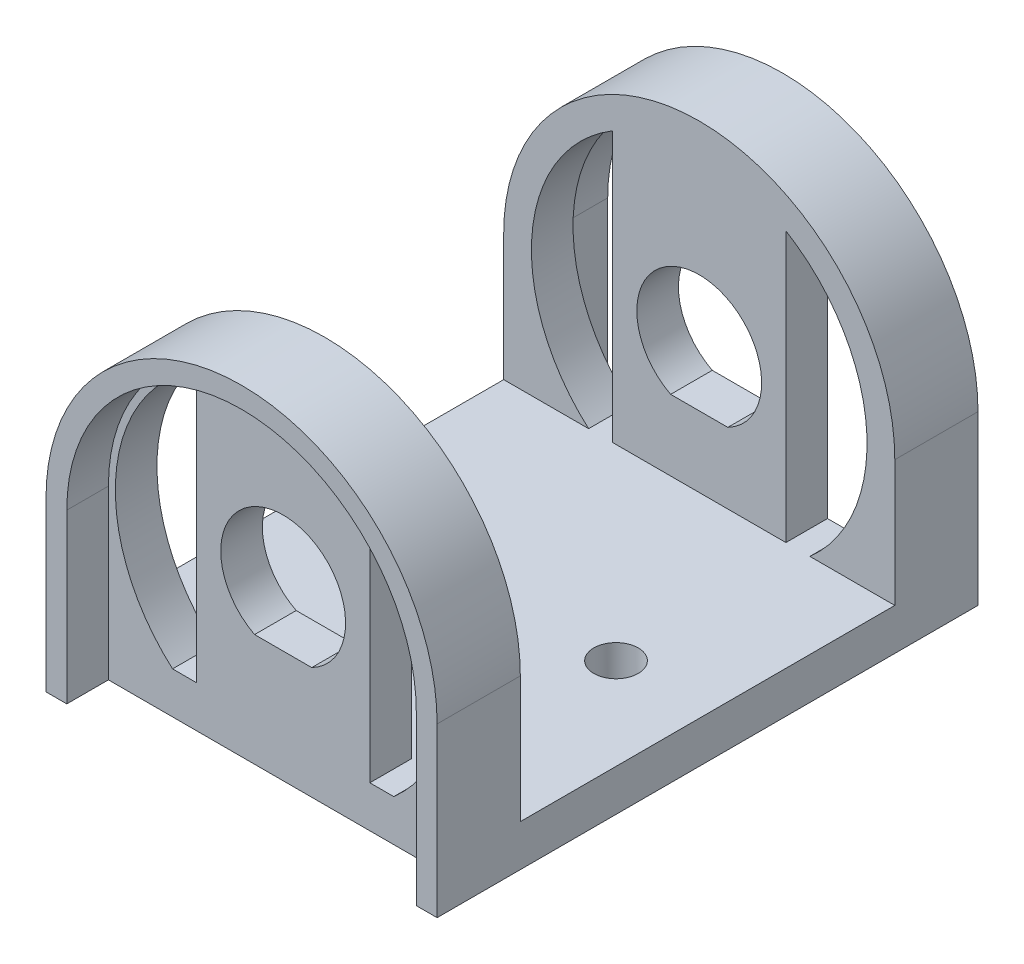
SolidWorks part; units mm, degrees
ref_plane "Front Plane" through (0, 0, 0) normal (0, 0, 1) x (1, 0, 0)
ref_plane "Top Plane" through (0, 0, 0) normal (0, 1, 0) x (1, 0, 0)
ref_plane "Right Plane" through (0, 0, 0) normal (1, 0, 0) x (0, 0, -1)
sketch "Sketch2" plane through (0, 0, 0) normal (0, 0, 1) x (1, 0, 0)
  line L0 (2, -4.75) -> (-2, -4.75) construction
  line L1 (-14.1, -13.1) -> (14.1, -13.1)
  line L3 (-14.1, 13.1) -> (14.1, 13.1) construction
  line L6 (0, -55) -> (0, 55) construction
  line L7 (2, -4.75) -> (-2, -4.75) construction
  line L8 (2.4495, -6.75) -> (-2.4495, -6.75) construction
  line L9 (6.25, 9.3609) -> (6.25, -10.1)
  line L10 (-6.25, 9.3609) -> (-6.25, -10.1)
  line L11 (7.975, -10.1) -> (6.25, -10.1)
  line L12 (-6.25, -10.1) -> (-7.975, -10.1)
  line L13 (2.0616, -5) -> (-2.0616, -5)
  line L27 (-14.1, 13.1) -> (14.1, -13.1) construction
  line L32 (14.1, 13.1) -> (-14.1, -13.1) construction
  line L35 (-14.1, -13.1) -> (-14.1, -1)
  line L36 (14.1, -13.1) -> (14.1, -1)
  line L37 (14.1, -1) -> (14.1, -13.1) construction
  line L38 (-14.1, -1) -> (-14.1, -13.1) construction
  arc A4 (14.1, -1) -> (-14.1, -1) centre (0, -1) ccw
  arc A7 (7.975, -10.1) -> (6.25, 9.3609) centre (0, -1) ccw
  circle A8 centre (0, -1) radius 14.1 construction
  arc A9 (2, -4.75) -> (-2, -4.75) centre (0, -1) ccw construction
  arc A10 (2, -4.75) -> (-2, -4.75) centre (0, -1) ccw construction
  circle A11 centre (0, -1) radius 12.1 construction
  arc A12 (2.4495, -6.75) -> (-2.4495, -6.75) centre (0, -1) ccw construction
  arc A13 (-6.25, 9.3609) -> (-7.975, -10.1) centre (0, -1) ccw
  arc A14 (2.0616, -5) -> (-2.0616, -5) centre (0, -1) ccw
  point P0 (0, 0)
  dimension "D5" = 24.2
  dimension "D6" = 0.25
  dimension "D1" = 28.2
  dimension "D2" = 26.2
  dimension "D4" = 2
  dimension "D3" = 2
extrude "Boss-Extrude2" add sketch "Sketch2" along normal mid plane 39 contours L36 A4 L35 L1 A7 L11
sketch "Sketch3" plane through (0, 0, 19.5) normal (0, 0, 1) x (1, 0, 0)
  line L2 (-12.1, -1) -> (-12.1, -13.1) construction
  line L9 (12.1, -1) -> (12.1, -13.1) construction
  line L15 (-12.6, -1) -> (-12.6, -13.1)
  line L16 (12.6, -1) -> (12.6, -13.1)
  line L17 (-12.6, -13.1) -> (12.6, -13.1)
  arc A0 (7.975, -10.1) -> (6.25, 9.3609) centre (0, -1) ccw construction
  arc A5 (12.1, -1) -> (-12.1, -1) centre (0, -1) ccw construction
  arc A7 (12.6, -1) -> (-12.6, -1) centre (0, -1) ccw
  dimension "D1" = 0.5
sketch "Sketch4" plane through (0, 0, 0) normal (1, 0, 0) x (0, 0, -1)
  line L0 (13.5, 13.1) -> (13.5, -10.1)
  line L1 (19.5, 13.1) -> (-19.5, 13.1) construction
  line L2 (13.5, -10.1) -> (-13.5, -10.1)
  line L3 (0, 55) -> (0, -55) construction
  line L4 (19.5, -1) -> (19.5, 13.1) construction
  line L5 (-19.5, -13.1) -> (19.5, -13.1) construction
  line L6 (13.5, 13.1) -> (-13.5, 13.1)
  line L7 (-13.5, 13.1) -> (-13.5, -10.1)
  point P13 (0, -10.1)
  point P14 (0, 13.1)
  dimension "D1" = 6
  dimension "D2" = 3
extrude "Cut-Extrude2" cut sketch "Sketch4" against normal through all both and the other way through all
sketch "Sketch5" plane through (0, 0, 0) normal (0, 1, 0) x (1, 0, 0)
  line L0 (-14.41, 0) -> (14.41, 0) construction
  line L1 (0, -14.41) -> (0, 14.41) construction
  circle A0 centre (7.5, 0) radius 1.6
  circle A1 centre (-7.5, 0) radius 1.6
  dimension "D1" = 3.2
  dimension "D2" = 7.5
extrude "Cut-Extrude4" cut sketch "Sketch3" against normal blind 3
extrude "Cut-Extrude5" cut sketch "Sketch5" against normal through all both and the other way through all
mirror "Mirror2" about plane through (0, 0, 0) normal (0, 0, 1) of "Cut-Extrude4"
